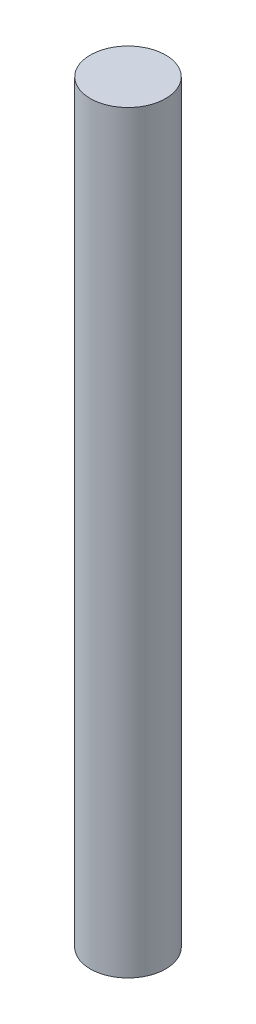
SolidWorks part; units mm, degrees
ref_plane "Front Plane" through (0, 0, 0) normal (0, 0, 1) x (1, 0, 0)
ref_plane "Top Plane" through (0, 0, 0) normal (0, 1, 0) x (1, 0, 0)
ref_plane "Right Plane" through (0, 0, 0) normal (1, 0, 0) x (0, 0, -1)
sketch "Sketch1" plane through (0, 0, 0) normal (0, 1, 0) x (1, 0, 0)
  circle A0 centre (0, 0) radius 0.127
  dimension "D1" = 0.254
extrude "Boss-Extrude1" add sketch "Sketch1" along normal blind 2.54
